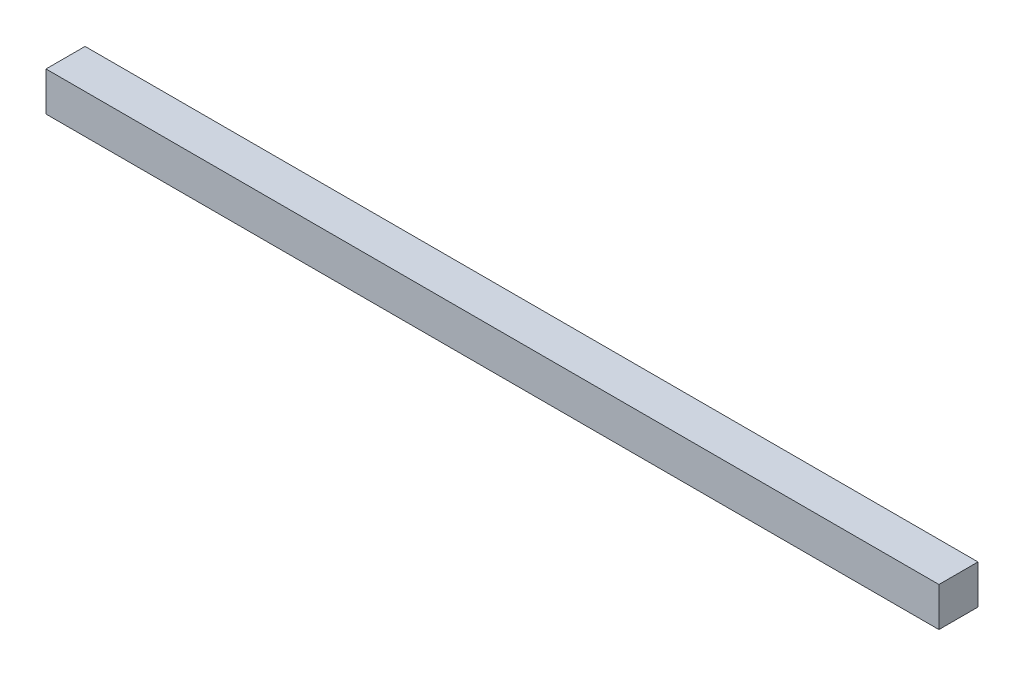
SolidWorks part; units mm, degrees
ref_plane "Front Plane" through (0, 0, 0) normal (0, 0, 1) x (1, 0, 0)
ref_plane "Top Plane" through (0, 0, 0) normal (0, 1, 0) x (1, 0, 0)
ref_plane "Right Plane" through (0, 0, 0) normal (1, 0, 0) x (0, 0, -1)
sketch "Sketch1" plane through (0, 0, 0) normal (0, 1, 0) x (1, 0, 0)
  line L0 (-114.265, 5) -> (114.265, -5) construction
  line L1 (-114.265, 5) -> (114.265, 5)
  line L2 (-114.265, 5) -> (-114.265, -5)
  line L3 (-114.265, -5) -> (114.265, -5)
  line L4 (114.265, 5) -> (114.265, -5)
  dimension "D1" = 228.53
  dimension "D2" = 10
extrude "Boss-Extrude1" add sketch "Sketch1" along normal blind 10
